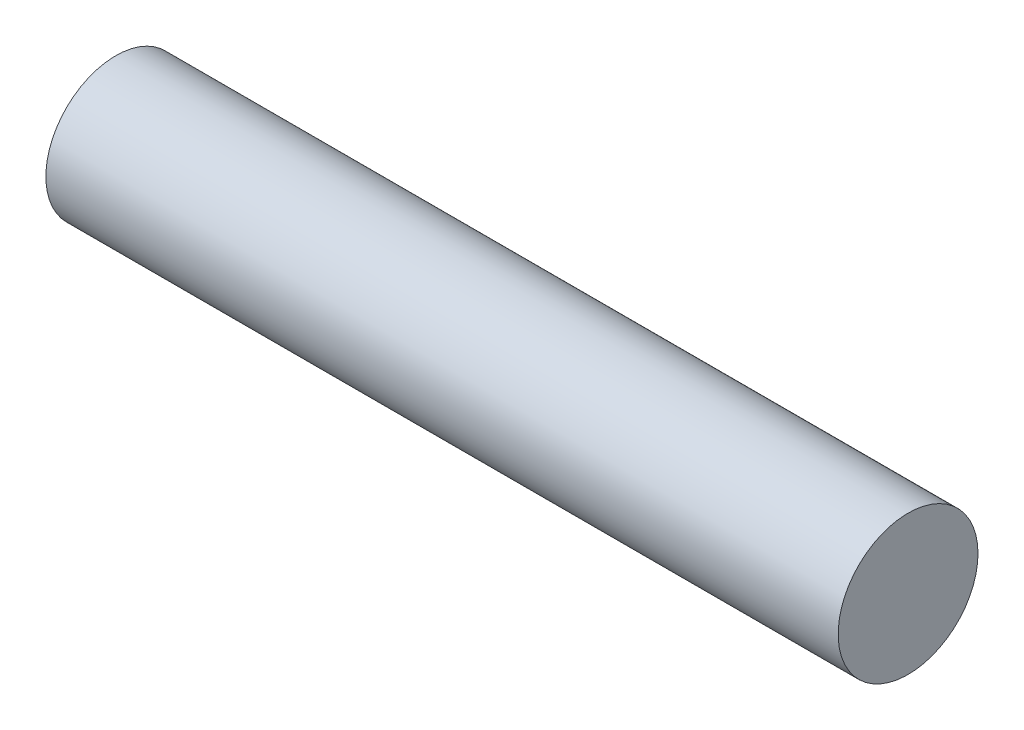
SolidWorks part; units mm, degrees
material "Plain Carbon Steel"
ref_plane "Front Plane" through (0, 0, 0) normal (0, 0, 1) x (1, 0, 0)
ref_plane "Top Plane" through (0, 0, 0) normal (0, 1, 0) x (1, 0, 0)
ref_plane "Right Plane" through (0, 0, 0) normal (1, 0, 0) x (0, 0, -1)
sketch "Sketch1" plane through (0, 0, 0) normal (1, 0, 0) x (0, 0, -1)
  circle A0 centre (0, 0) radius 19.05
extrude "Boss-Extrude1" add sketch "Sketch1" along normal mid plane 215.9
